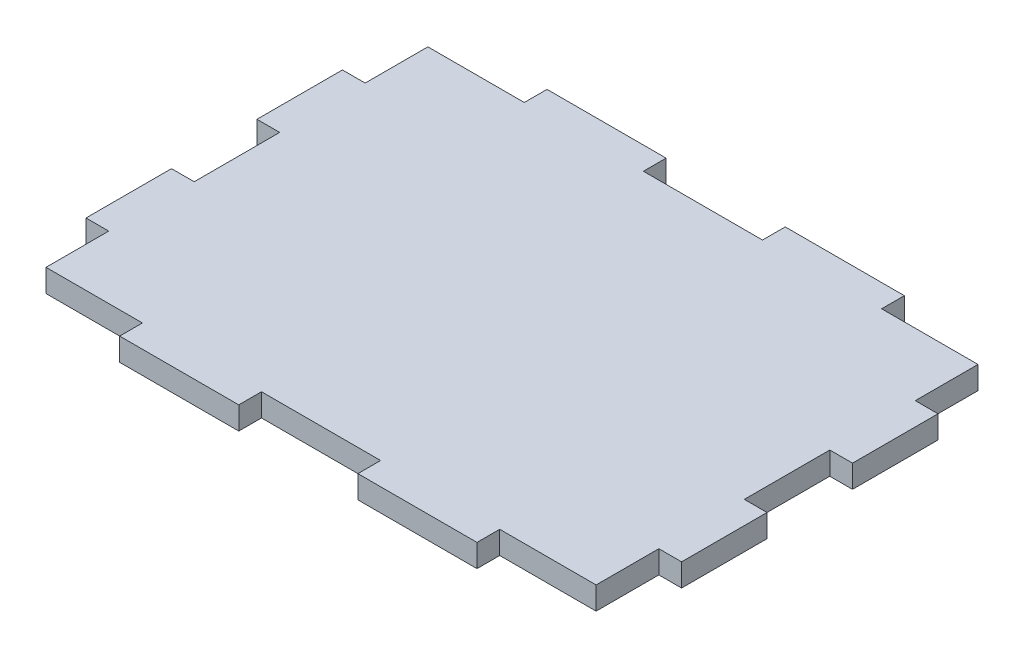
SolidWorks part; units mm, degrees
ref_plane "Front Plane" through (0, 0, 0) normal (0, 0, 1) x (1, 0, 0)
ref_plane "Top Plane" through (0, 0, 0) normal (0, 1, 0) x (1, 0, 0)
ref_plane "Right Plane" through (0, 0, 0) normal (1, 0, 0) x (0, 0, -1)
sketch "Sketch1" plane through (0, 0, 0) normal (0, 1, 0) x (1, 0, 0)
  line L1 (-41.5925, -29.845) -> (41.5925, -29.845)
  line L2 (-41.5925, -29.845) -> (-41.5925, 29.845)
  line L3 (-41.5925, 29.845) -> (41.5925, 29.845)
  line L4 (41.5925, -29.845) -> (41.5925, 29.845)
  line L5 (-41.5925, -29.845) -> (41.5925, 29.845) construction
  line L6 (-41.5925, 29.845) -> (41.5925, -29.845) construction
  point P0 (0, 0)
  dimension "D1" = 83.185
  dimension "D2" = 59.69
extrude "Boss-Extrude1" add sketch "Sketch1" along normal blind 3.175
sketch "Sketch2" plane through (0, 3.175, 0) normal (0, 1, 0) x (1, 0, 0)
  line L1 (-41.5925, 29.845) -> (-24.9555, 29.845)
  line L2 (-41.5925, 29.845) -> (-41.5925, 26.67)
  line L3 (-41.5925, 26.67) -> (-24.9555, 26.67)
  line L4 (-24.9555, 29.845) -> (-24.9555, 26.67)
  line L5 (-41.5925, -29.845) -> (-24.9555, -29.845)
  line L6 (-41.5925, -29.845) -> (-41.5925, -26.67)
  line L7 (-41.5925, -26.67) -> (-24.9555, -26.67)
  line L8 (-24.9555, -29.845) -> (-24.9555, -26.67)
  dimension "D1" = 16.637
  dimension "D2" = 3.175
  dimension "D3" = 3.175
extrude "Cut-Extrude1" cut sketch "Sketch2" against normal blind 3.175
pattern_linear "LPattern1" count 3 spacing 33.274 along (1, 0, 0) of "Cut-Extrude1"
sketch "Sketch3" plane through (0, 3.175, 0) normal (0, 1, 0) x (1, 0, 0)
  line L1 (-41.5925, -29.845) -> (41.5925, -29.845) construction
  line L2 (-41.5925, -29.845) -> (-41.5925, 29.845) construction
  line L3 (-41.5925, 29.845) -> (41.5925, 29.845) construction
  line L4 (41.5925, -29.845) -> (41.5925, 29.845) construction
  line L5 (-41.5925, -29.845) -> (41.5925, 29.845) construction
  line L6 (-41.5925, 29.845) -> (41.5925, -29.845) construction
  line L7 (-41.5925, 29.845) -> (-38.4175, 29.845)
  line L8 (-41.5925, 29.845) -> (-41.5925, 17.907)
  line L9 (-41.5925, 17.907) -> (-38.4175, 17.907)
  line L10 (-38.4175, 29.845) -> (-38.4175, 17.907)
  line L11 (41.5925, 29.845) -> (38.4175, 29.845)
  line L12 (41.5925, 29.845) -> (41.5925, 17.907)
  line L13 (41.5925, 17.907) -> (38.4175, 17.907)
  line L14 (38.4175, 29.845) -> (38.4175, 17.907)
  point P0 (0, 0)
  dimension "D1" = 83.185
  dimension "D2" = 59.69
  dimension "D3" = 3.175
  dimension "D4" = 11.938
  dimension "D5" = 3.175
extrude "Cut-Extrude2" cut sketch "Sketch3" against normal blind 3.175
pattern_linear "LPattern4" count 3 spacing 23.876 along (0, 0, 1) of "Cut-Extrude2"
